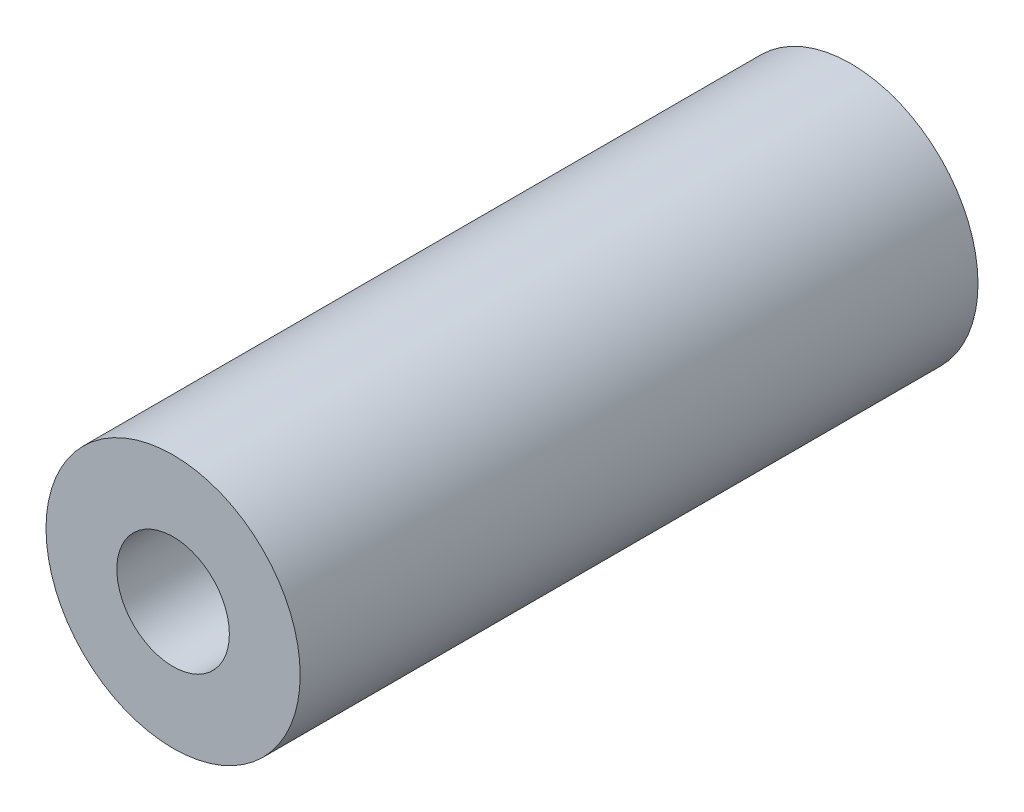
SolidWorks part; units mm, degrees
ref_plane "Front Plane" through (0, 0, 0) normal (0, 0, 1) x (1, 0, 0)
ref_plane "Top Plane" through (0, 0, 0) normal (0, 1, 0) x (1, 0, 0)
ref_plane "Right Plane" through (0, 0, 0) normal (1, 0, 0) x (0, 0, -1)
sketch "Sketch1" plane through (0, 0, 0) normal (0, 0, 1) x (1, 0, 0)
  line L0 (0, 2.1082) -> (0, 4.7625) construction
  line L1 (0, -2.1082) -> (0, -4.7625) construction
  circle A0 centre (0, 0) radius 4.7625
  circle A1 centre (0, 0) radius 2.1082
  dimension "OD" = 9.525
  dimension "ID" = 4.2164
sketch "Sketch2" plane through (0, 0, 0) normal (1, 0, 0) x (0, 0, -1)
  line L0 (-12.7, 2.1082) -> (12.7, 2.1082) construction
  line L1 (-12.7, -2.1082) -> (12.7, -2.1082) construction
  line L2 (-12.7, -4.7625) -> (12.7, -4.7625) construction
  line L3 (-12.7, 4.7625) -> (12.7, 4.7625) construction
  dimension "Length" = 25.4
extrude "Extrude1" add sketch "Sketch1" along normal up to vertex (12.7 mm away) and the other way up to vertex (12.7 mm away) up to point (0, 2.1082, 12.7) other way up to point (0, 2.1082, -12.7)
sketch "Sketch3" plane through (0, 0, 12.7) normal (0, 0, 1) x (1, 0, 0)
  circle A0 centre (0, 0) radius 2.1082 construction
  circle A3 centre (0, 0) radius 2.1082
  point P3 (-2.1082, 0)
